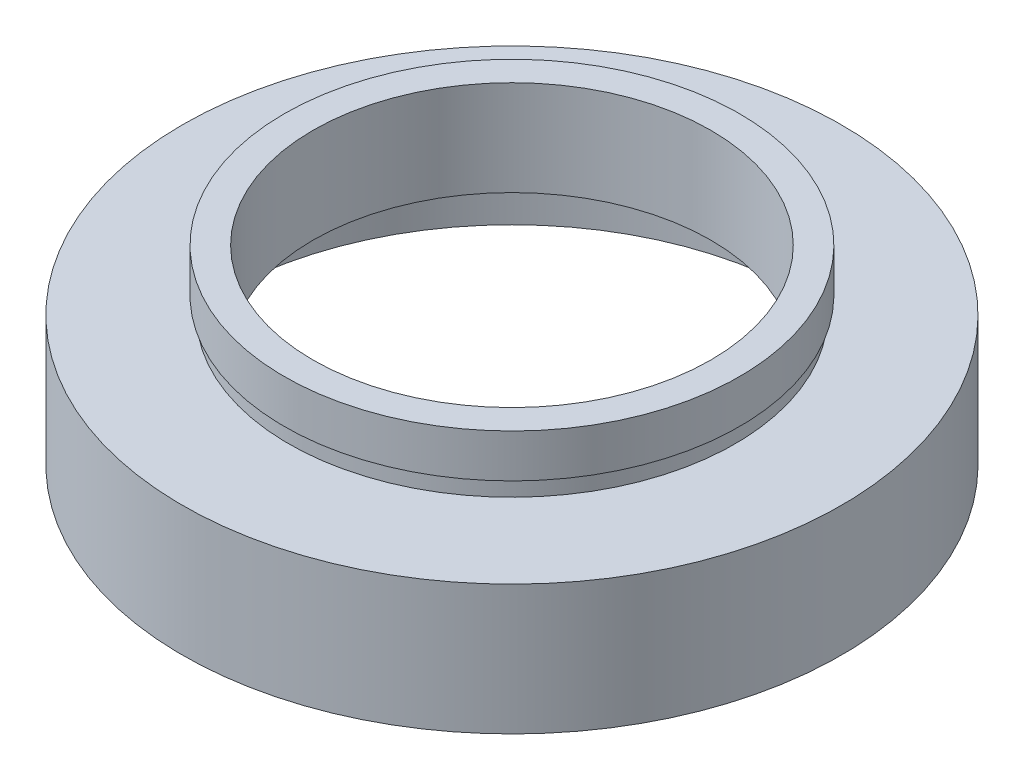
SolidWorks part; units mm, degrees
ref_plane "前视基准面" through (0, 0, 0) normal (0, 0, 1) x (1, 0, 0)
ref_plane "上视基准面" through (0, 0, 0) normal (0, 1, 0) x (1, 0, 0)
ref_plane "右视基准面" through (0, 0, 0) normal (1, 0, 0) x (0, 0, -1)
sketch "草图1" plane through (0, 0, 0) normal (0, 0, 1) x (1, 0, 0)
  line L0 (0, 16.886) -> (0, -24.4878) construction
  line L1 (17, 0) -> (17, 4.5)
  line L2 (11.5, 5.5) -> (17.6, 5.5)
  line L3 (11.5, 5.5) -> (11.5, 11)
  line L4 (11.5, 11) -> (13.16, 11)
  line L5 (13.16, 11) -> (13.16, 8.5)
  line L6 (13.16, 8.5) -> (12.9, 8.5)
  line L7 (12.9, 8.5) -> (12.9, 7.5)
  line L8 (12.9, 7.5) -> (19.05, 7.5)
  line L9 (19.05, 7.5) -> (19.05, 0)
  line L10 (19.05, 0) -> (17, 0)
  line L11 (17, 4.5) -> (17.6, 4.5)
  line L12 (17.6, 4.5) -> (17.6, 5.5)
  line L13 (0, 0) -> (3.4668, 0) construction
  point P4 (18.025, 0)
  dimension "D1" = 11.5
  dimension "D2" = 13.16
  dimension "D3" = 12.9
  dimension "D4" = 17
  dimension "D5" = 17.6
  dimension "D6" = 19.05
  dimension "D7" = 11
  dimension "D8" = 7.5
  dimension "D9" = 1
  dimension "D10" = 4.5
  dimension "D11" = 1
revolve "旋转1" add sketch "草图1" angle 360 about L0
cosmetic thread "装饰螺纹线1" parameters "D2"=26.29
cosmetic thread "装饰螺纹线2" parameters "D2"=23.2
cosmetic thread "装饰螺纹线3" parameters "D2"=35
